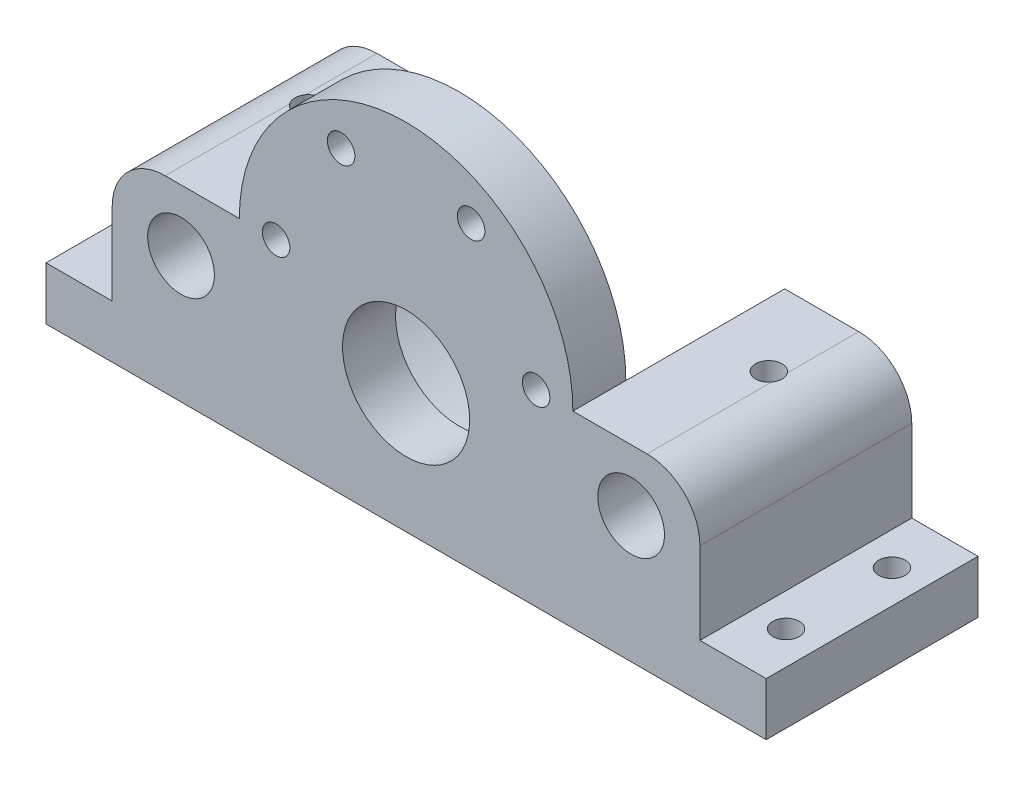
SolidWorks part; units mm, degrees
ref_plane "Front Plane" through (0, 0, 0) normal (0, 0, 1) x (1, 0, 0)
ref_plane "Top Plane" through (0, 0, 0) normal (0, 1, 0) x (1, 0, 0)
ref_plane "Right Plane" through (0, 0, 0) normal (1, 0, 0) x (0, 0, -1)
sketch "Sketch1" plane through (0, 0, 0) normal (0, 0, 1) x (1, 0, 0)
  line L1 (43.18, 3.175) -> (-43.18, 3.175)
  line L2 (43.18, 3.175) -> (43.18, -3.175)
  line L3 (43.18, -3.175) -> (-43.18, -3.175)
  line L4 (-43.18, 3.175) -> (-43.18, -3.175)
  line L5 (43.18, 3.175) -> (-43.18, -3.175) construction
  line L6 (43.18, -3.175) -> (-43.18, 3.175) construction
  point P0 (0, 0)
  dimension "D1" = 6.35
  dimension "D2" = 86.36
extrude "Boss-Extrude1" add sketch "Sketch1" along normal blind 25.4
sketch "Sketch2" plane through (0, 0, 25.4) normal (0, 0, 1) x (1, 0, 0)
  line L0 (-43.18, -0.635) -> (43.18, -0.635) construction
  line L1 (-43.18, 3.175) -> (-43.18, -3.175) construction
  line L2 (43.18, -3.175) -> (43.18, 3.175) construction
  line L3 (-43.18, -3.175) -> (43.18, -3.175) construction
  line L4 (-20, 19.365) -> (-20, 3.175)
  line L5 (43.18, 3.175) -> (-43.18, 3.175) construction
  line L6 (20, 19.365) -> (20, 3.175)
  line L7 (-20, 3.175) -> (-11.7424, 3.175)
  line L8 (11.7424, 3.175) -> (20, 3.175)
  circle A0 centre (0, 19.365) radius 20
  line M6 (43.18, 3.175) -> (-43.18, 3.175)
  dimension "D2" = 40
  dimension "D1" = 2.54
extrude "Boss-Extrude2" add sketch "Sketch2" against normal blind 25.4 contours A0 M6 | A0 L4 M6 | A0 L6 M6
sketch "Sketch3" plane through (0, 0, 25.4) normal (0, 0, 1) x (1, 0, 0)
  line L0 (-15.5885, 19.365) -> (-7.7942, 32.7558) construction
  line L1 (7.7942, 32.7558) -> (15.5885, 19.365) construction
  line L2 (-15.5885, 19.365) -> (15.5885, 19.365) construction
  line L3 (-15.5885, 19.365) -> (-7.7942, 5.9742) construction
  line L4 (15.5885, 19.365) -> (7.7942, 5.9742) construction
  line L5 (-7.7942, 32.7558) -> (7.7942, 32.7558) construction
  line L6 (-7.7942, 5.9742) -> (7.7942, 5.9742) construction
  line L7 (-7.7942, 32.7558) -> (-7.7942, 5.9742) construction
  circle A0 centre (0, 19.365) radius 20 construction
  arc A1 (20, 19.365) -> (-20, 19.365) centre (0, 19.365) ccw construction
  circle A2 centre (0, 12.253) radius 7.62
  circle A3 centre (-7.7942, 32.7558) radius 1.651
  circle A4 centre (7.7942, 32.7558) radius 1.651
  circle A5 centre (-15.5885, 19.365) radius 1.651
  circle A8 centre (15.5885, 19.365) radius 1.651
  point P11 (0, 5.9742)
  point P14 (0, 32.7558)
  point P15 (0, 19.365)
  point P16 (-7.7942, 19.365)
  dimension "D1" = 15.24
  dimension "D5" = 3.302
  dimension "D2" = 15.494
  dimension "D3" = 30.988
  dimension "D4" = 15.5885
  dimension "D6" = 7.112
extrude "Cut-Extrude3" cut sketch "Sketch3" against normal blind 25.4
sketch "Sketch4" plane through (0, 0, 0) normal (0, 0, -1) x (-1, 0, 0)
  circle A0 centre (0, 19.365) radius 20
  arc A1 (20, 19.365) -> (-20, 19.365) centre (0, 19.365) ccw construction
extrude "Cut-Extrude4" cut sketch "Sketch4" against normal blind 19.05
sketch "Sketch6" plane through (0, 0, 0) normal (0, 0, -1) x (-1, 0, 0)
  line L0 (20, 19.365) -> (20, 3.175) construction
  line L1 (-20, 19.365) -> (20, 19.365)
  line L2 (-20, 19.365) -> (-20, 9.205)
  line L3 (-20, 9.205) -> (20, 9.205)
  line L4 (20, 19.365) -> (20, 9.205)
  dimension "D1" = 10.16
extrude "Cut-Extrude6" cut sketch "Sketch6" against normal up to surface (19.05 mm away) up to face at (0, 19.365, 19.05)
sketch "Sketch7" plane through (0, 0, 25.4) normal (0, 0, 1) x (1, 0, 0)
  line L0 (-20, 3.175) -> (-43.18, 3.175) construction
  line L1 (-20, 3.175) -> (-35.24, 3.175)
  line L2 (-20, 3.175) -> (-20, 19.365)
  line L3 (-20, 19.365) -> (-35.24, 19.365)
  line L4 (-35.24, 3.175) -> (-35.24, 19.365)
  line L5 (-20, 19.365) -> (-20, 3.175) construction
  circle A0 centre (-26.9875, 11.999) radius 4
  circle A1 centre (0, 12.253) radius 7.62 construction
  point P11 (-27.62, 10.1746)
  point P13 (-27.4463, 12.253)
  dimension "D1" = 8
  dimension "D2" = 15.24
  dimension "D3" = 0.254
  dimension "D4" = 26.9875
extrude "Boss-Extrude3" add sketch "Sketch7" against normal up to surface (25.4 mm away)
mirror "Mirror2" about plane through (0, 0, 0) normal (1, 0, 0) of "Boss-Extrude3"
fillet "Fillet1" radius 6.35 2 edges at (-35.24, 19.365, 12.7) (35.24, 19.365, 12.7)
sketch "Sketch9" plane through (0, 3.175, 0) normal (0, 1, 0) x (1, 0, 0)
  line L0 (-39.21, -6.35) -> (-39.21, -19.05) construction
  line L1 (-43.18, -12.7) -> (-35.24, -12.7) construction
  line L2 (-43.18, -25.4) -> (-43.18, 0) construction
  line L3 (-35.24, 0) -> (-35.24, -25.4) construction
  line L4 (-35.24, 0) -> (-43.18, 0) construction
  circle A0 centre (-39.21, -6.35) radius 1.5875
  circle A1 centre (-39.21, -19.05) radius 1.5875
  point P10 (-39.21, -12.7)
  point P11 (-39.21, -12.7)
  point P13 (-35.24, -12.7)
  dimension "D1" = 3.175
  dimension "D2" = 6.35
extrude "Cut-Extrude7" cut sketch "Sketch9" against normal through all
mirror "Mirror3" about plane through (0, 0, 0) normal (1, 0, 0) of "Cut-Extrude7"
sketch "Sketch11" plane through (0, 19.365, 0) normal (0, 1, 0) x (1, 0, 0)
  line L0 (-20, -9.525) -> (-35.24, -9.525) construction
  line L1 (-20, 0) -> (-20, -19.05) construction
  line L2 (-35.24, 0) -> (-35.24, -25.4) construction
  circle A0 centre (-27.62, -9.525) radius 1.5875
  point P6 (-20, -9.525)
  dimension "D1" = 3.175
extrude "Cut-Extrude8" cut sketch "Sketch11" against normal up to next
mirror "Mirror4" about plane through (0, 0, 0) normal (1, 0, 0) of "Cut-Extrude8"
